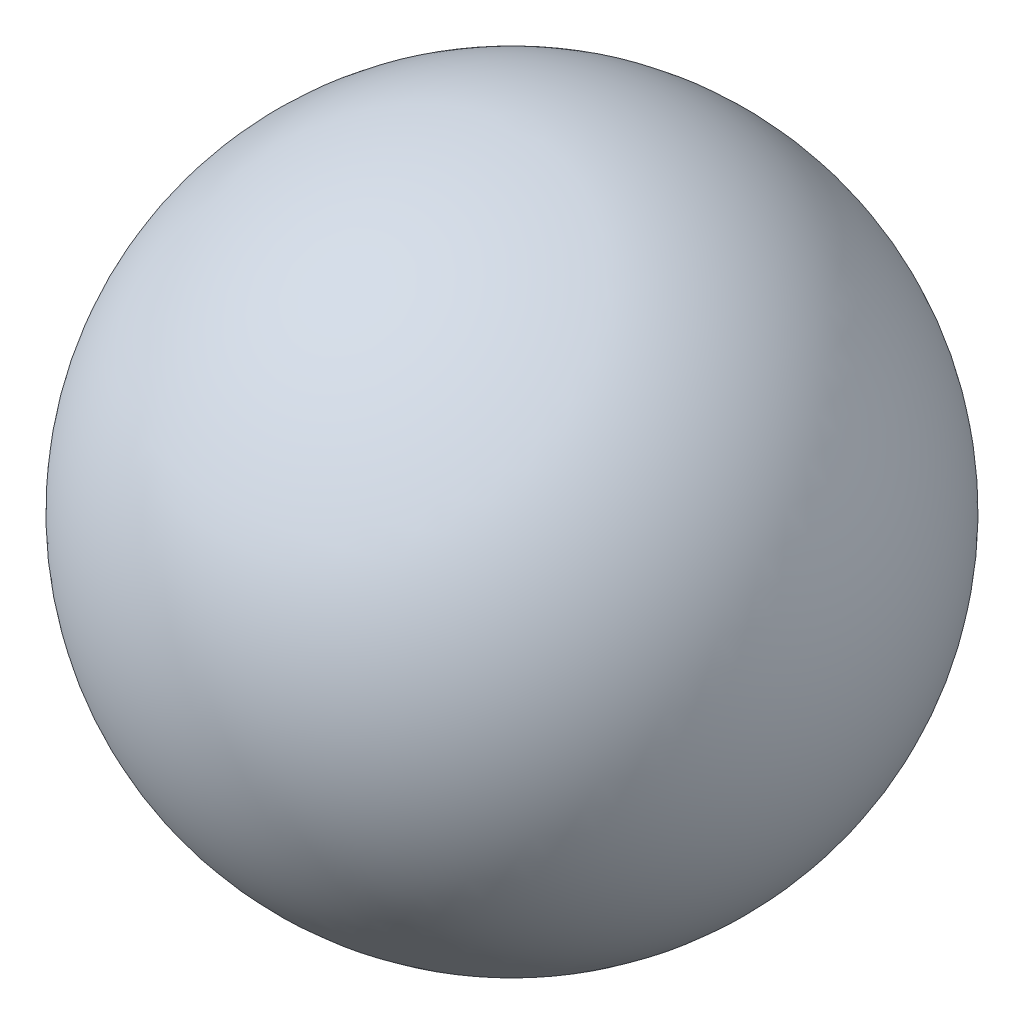
SolidWorks part; units mm, degrees
ref_plane "Front Plane" through (0, 0, 0) normal (0, 0, 1) x (1, 0, 0)
ref_plane "Top Plane" through (0, 0, 0) normal (0, 1, 0) x (1, 0, 0)
ref_plane "Right Plane" through (0, 0, 0) normal (1, 0, 0) x (0, 0, -1)
sketch "Sketch1" plane through (0, 0, 0) normal (1, 0, 0) x (0, 0, -1)
  line L0 (0, 141.1371) -> (0, -11.2629) construction
  line L1 (0, 141.1371) -> (0, 139.6371)
  line L2 (39.87, 0) -> (39.87, 6)
  line L3 (39.87, 6) -> (31.75, 6)
  line L4 (31.75, 6) -> (31.75, 10)
  line L5 (31.75, 10) -> (50.6163, 10)
  line L6 (39.37, 6) -> (39.37, 0) construction
  arc A0 (0, 141.1371) -> (39.87, 0) centre (0, 64.9371) cw
  arc A1 (0, 139.6371) -> (50.6163, 10) centre (0, 64.9371) cw
  point P12 (34.8771, 0)
  point P15 (0, 0)
  point P18 (51.2443, 11.3481)
  point P19 (0, 0)
  dimension "D1" = 152.4
  dimension "D2" = 0.5
  dimension "D3" = 1.5
  dimension "D4" = 6
  dimension "D5" = 39.37
  dimension "D6" = 63.5
  dimension "D7" = 4
revolve "Revolve1" add sketch "Sketch1" angle 360 about L0
sketch "Sketch2" plane through (0, 6, 0) normal (0, -1, 0) x (1, 0, 0)
  circle A0 centre (0, 35.56) radius 1.5 construction
  circle A1 centre (0, 35.56) radius 1.9
  circle A2 centre (35.56, 0) radius 1.5 construction
  circle A3 centre (0, -35.56) radius 1.5 construction
  circle A4 centre (-35.56, 0) radius 1.5 construction
  circle A5 centre (35.56, 0) radius 1.9
  circle A6 centre (0, -35.56) radius 1.9
  circle A7 centre (-35.56, 0) radius 1.9
  point P2 (0, 0)
  point P13 (0, 0)
  point P20 (0, 0)
  dimension "D1" = 3
  dimension "D3" = 0.4
  dimension "D2" = 35.56
  dimension "D4" = 4
  dimension "D5" = 4
extrude "Cut-Extrude1" cut sketch "Sketch2" against normal blind 2.54
